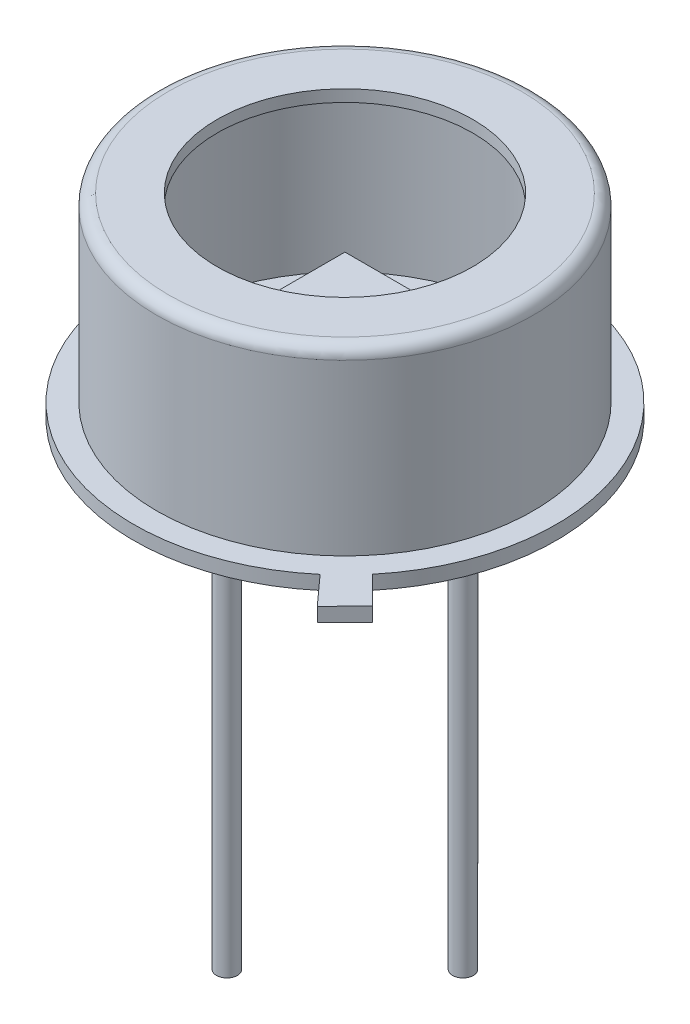
SolidWorks part; units mm, degrees
ref_plane "Front Plane" through (0, 0, 0) normal (0, 0, 1) x (1, 0, 0)
ref_plane "Top Plane" through (0, 0, 0) normal (0, 1, 0) x (1, 0, 0)
ref_plane "Right Plane" through (0, 0, 0) normal (1, 0, 0) x (0, 0, -1)
sketch "Sketch1" plane through (0, 0, 0) normal (0, 0, 1) x (1, 0, 0)
  line L0 (0, 0) -> (0, 37.7864) construction
  line L2 (4.55, 0) -> (4.55, 0.3)
  line L3 (4.55, 0.3) -> (4.05, 0.3)
  line L6 (4.05, 0.3) -> (4.05, 3.946)
  line L7 (3.796, 4.2) -> (2.75, 4.2)
  arc A0 (4.05, 3.946) -> (3.796, 4.2) centre (3.796, 3.946) ccw
  dimension "D7" = 0.254
  dimension "D1" = 0.3
  dimension "D2" = 8.1
  dimension "D4" = 9.1
  dimension "D6" = 4.2
  dimension "D8" = 5.5
revolve "Revolve-Thin2" add sketch "Sketch1" angle 360 about L0
sketch "Sketch2" plane through (0, 0, 0) normal (0, -1, 0) x (1, 0, 0)
  circle A1 centre (0, 0) radius 4.55
  circle A2 centre (0, 0) radius 4.55
  dimension "D1" = 0
extrude "Boss-Extrude1" add sketch "Sketch2" against normal up to surface (0.046 mm away) up to face at (0, 0.046, -3.796)
sketch "Sketch3" plane through (0, 0, 0) normal (0, -1, 0) x (1, 0, 0)
  line L0 (1, 1) -> (-1, -1) construction
  line L1 (-1, 1) -> (1, 1)
  line L2 (-1, 1) -> (-1, -1)
  line L3 (-1, -1) -> (1, -1)
  line L4 (1, 1) -> (1, -1)
  dimension "D1" = 2
extrude "Boss-Extrude2" add sketch "Sketch3" along normal blind 0.508 from offset 2.1 separate body offset against normal yes
sketch "Sketch4" plane through (0, 0, 0) normal (0, -1, 0) x (1, 0, 0)
  line L0 (-4.55, 0) -> (0, 0) construction
  line L5 (0, 0) -> (3.8001, 3.8001) construction
  line L6 (0, 0) -> (4.5545, 0) construction
  line L7 (3.4992, 2.9083) -> (2.9389, 3.4736)
  line L8 (3.4992, 2.9083) -> (4.0968, 3.5008)
  line L9 (4.0968, 3.5008) -> (3.5034, 4.0995)
  line L11 (3.5034, 4.0995) -> (2.9389, 3.4736)
  circle A0 centre (0, 0) radius 4.55 construction
  point P6 (-4.55, 0)
  dimension "D1" = 2.9389
  dimension "D2" = 3.5034
  dimension "D3" = 45
extrude "Boss-Extrude3" add sketch "Sketch4" against normal up to surface (0.3 mm away) up to face at (0, 0.3, -4.05)
sketch "Sketch5" plane through (0, 0, 0) normal (0, -1, 0) x (1, 0, 0)
  line L0 (0, 0) -> (0, 2.54) construction
  line L2 (-2.54, 0) -> (2.54, 0) construction
  circle A0 centre (0, 0) radius 2.54 construction
  circle A1 centre (-2.54, 0) radius 0.225
  circle A2 centre (2.54, 0) radius 0.225
  circle A3 centre (0, 2.54) radius 0.225
  dimension "D1" = 5.08
  dimension "D2" = 0.45
  dimension "D3" = 5.08
  dimension "D4" = 0.45
  dimension "D5" = 0.45
extrude "Boss-Extrude4" add sketch "Sketch5" along normal blind 9
sketch "Sketch7" plane through (0, 0, 0) normal (0, -1, 0) x (1, 0, 0)
  circle A0 centre (0, 2.54) radius 0.75
  dimension "D1" = 1.5
extrude "Boss-Extrude5" add sketch "Sketch7" along normal blind 0.4
